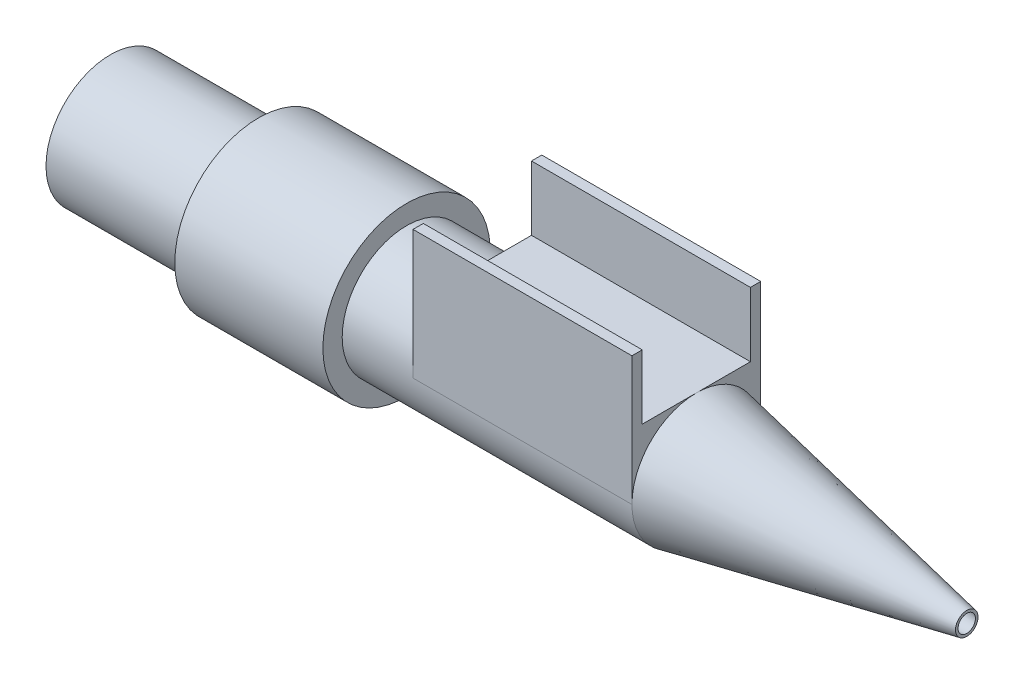
SolidWorks part; units mm, degrees
ref_plane "Přední rovina" through (0, 0, 0) normal (0, 0, 1) x (1, 0, 0)
ref_plane "Vrchní rovina" through (0, 0, 0) normal (0, 1, 0) x (1, 0, 0)
ref_plane "Pravá rovina" through (0, 0, 0) normal (1, 0, 0) x (0, 0, -1)
sketch "Skica1" plane through (0, 0, 0) normal (0, 0, 1) x (1, 0, 0)
  line L0 (0, 0) -> (75.6702, 0) construction
  line L1 (0, 0) -> (0, 5)
  line L2 (0, 5) -> (11.5, 5)
  line L3 (11.5, 5) -> (11.5, 6.5)
  line L4 (11.5, 6.5) -> (23, 6.5)
  line L5 (23, 6.5) -> (23, 5)
  line L6 (23, 5) -> (45.5, 5)
  line L7 (45.5, 5) -> (66.5, 0.875)
  line L8 (66.5, 0.875) -> (66.5, 0)
  line L9 (66.5, 0) -> (0, 0)
  point P11 (75.6702, 0)
  dimension "D1" = 10
  dimension "D2" = 13
  dimension "D3" = 10
  dimension "D4" = 11.5
  dimension "D5" = 11.5
  dimension "D6" = 22.5
  dimension "D7" = 66.5
  dimension "D8" = 1.75
revolve "Rotovat1" add sketch "Skica1" angle 360 about L0
sketch "Skica2" plane through (0, 0, 0) normal (0, 1, 0) x (1, 0, 0)
  line L0 (45.5, 5) -> (45.5, -5)
  line L1 (45.5, -5) -> (28.5, -5)
  line L2 (23, -5) -> (45.5, -5) construction
  line L3 (28.5, -5) -> (28.5, 5)
  line L4 (45.5, 5) -> (23, 5) construction
  line L5 (28.5, 5) -> (45.5, 5)
  dimension "D1" = 17
extrude "Přidat vysunutím1" add sketch "Skica2" along normal blind 5
sketch "Skica3" plane through (0, 5, 0) normal (0, 1, 0) x (1, 0, 0)
  line L0 (28.5, -5) -> (45.5, -5)
  line L1 (28.5, -5) -> (45.5, -5) construction
  line L2 (45.5, -5) -> (45.5, -4.2)
  line L3 (45.5, -5) -> (45.5, 0) construction
  line L4 (45.5, -4.2) -> (28.5, -4.2)
  line L5 (28.5, 0) -> (28.5, -5) construction
  line L6 (28.5, -4.2) -> (28.5, -5)
  line L7 (28.5, 5) -> (45.5, 5)
  line L8 (45.5, 5) -> (45.5, 4.2)
  line L9 (45.5, 0) -> (45.5, 5) construction
  line L10 (45.5, 4.2) -> (28.5, 4.2)
  line L11 (28.5, 5) -> (28.5, 0) construction
  line L12 (28.5, 4.2) -> (28.5, 5)
  dimension "D1" = 0.8
  dimension "D2" = 0.8
extrude "Přidat vysunutím2" add sketch "Skica3" along normal blind 5
sketch "Skica4" plane through (0, 0, 0) normal (0, 0, 1) x (1, 0, 0)
  line L0 (0, 0) -> (71.2547, 0) construction
  line L1 (0, 5) -> (0, -5) construction
  line L2 (0, 0) -> (0, 3.5)
  line L3 (0, 3.5) -> (45.5, 3.5)
  line L4 (45.5, 0) -> (45.5, 5) construction
  line L5 (45.5, 3.5) -> (66.5, 0.675)
  line L6 (66.5, -0.875) -> (66.5, 0.875) construction
  line L7 (66.5, 0.675) -> (66.5, 0)
  line L8 (66.5, 0) -> (0, 0)
  point P14 (66.5, 0.6036)
  dimension "D1" = 3.5
  dimension "D2" = 0.2
revolve "Odebrat rotací1" cut sketch "Skica4" angle 360 about L0
